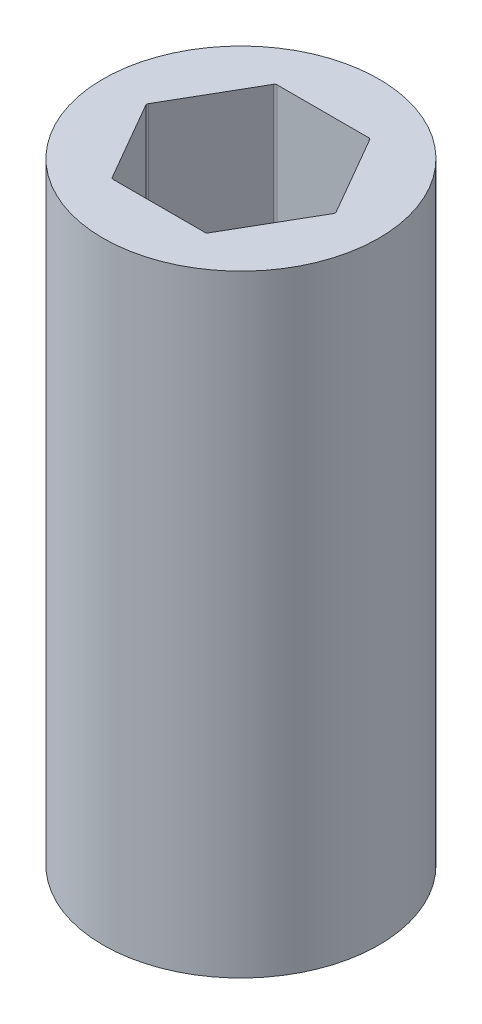
SolidWorks part; units mm, degrees
material "Nylon 101"
ref_plane "Front Plane" through (0, 0, 0) normal (0, 0, 1) x (1, 0, 0)
ref_plane "Top Plane" through (0, 0, 0) normal (0, 1, 0) x (1, 0, 0)
ref_plane "Right Plane" through (0, 0, 0) normal (1, 0, 0) x (0, 0, -1)
sketch "Sketch1" plane through (0, 0, 0) normal (0, 1, 0) x (1, 0, 0)
  line L1 (7.6256, 0) -> (3.8128, 6.604)
  line L2 (3.8128, 6.604) -> (-3.8128, 6.604)
  line L3 (-3.8128, 6.604) -> (-7.6256, 0)
  line L4 (-7.6256, 0) -> (-3.8128, -6.604)
  line L5 (-3.8128, -6.604) -> (3.8128, -6.604)
  line L6 (3.8128, -6.604) -> (7.6256, 0)
  circle A0 centre (0, 0) radius 11.1125
  circle A1 centre (0, 0) radius 6.604 construction
  dimension "D1" = 13.208
  dimension "D2" = 22.225
extrude "Boss-Extrude1" add sketch "Sketch1" along normal blind 49.3268
fillet "Fillet1" radius 0.2 6 edges at (3.8128, 24.6634, -6.604) (-3.8128, 24.6634, -6.604) (-7.6256, 24.6634, 0) (3.8128, 24.6634, 6.604) (7.6256, 24.6634, 0) (-3.8128, 24.6634, 6.604)
